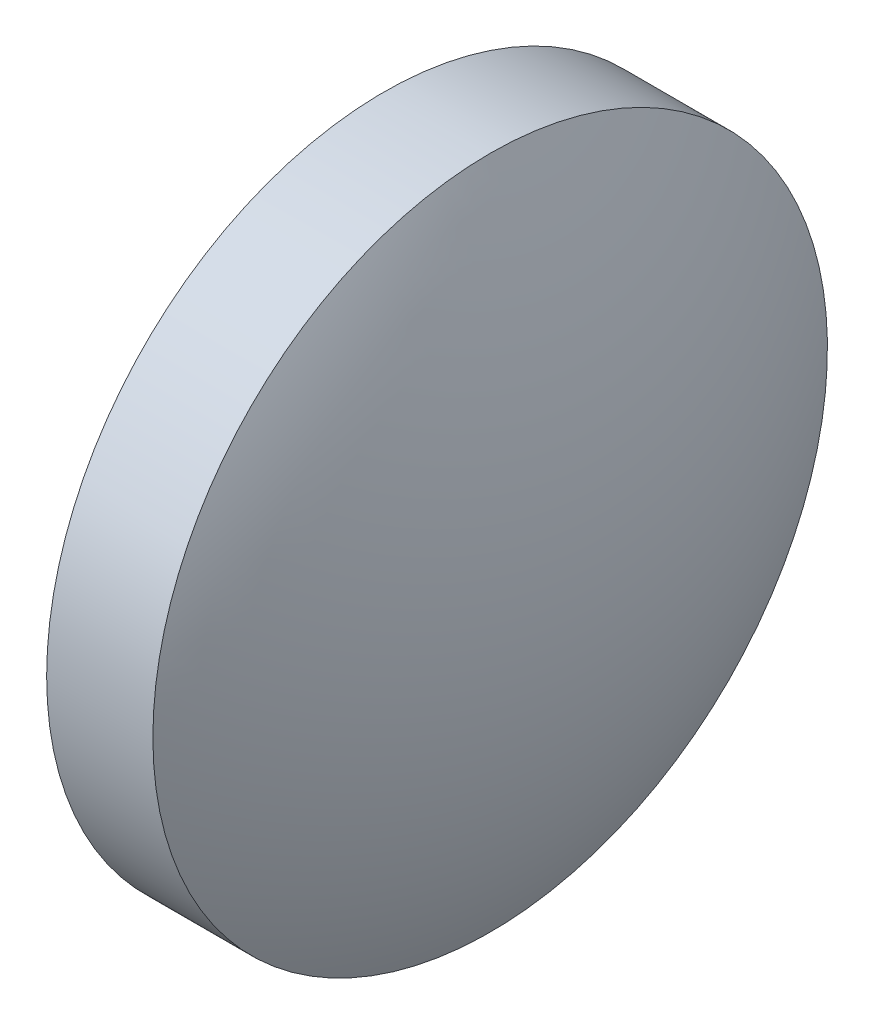
SolidWorks part; units mm, degrees
ref_plane "前视基准面" through (0, 0, 0) normal (0, 0, 1) x (1, 0, 0)
ref_plane "上视基准面" through (0, 0, 0) normal (0, 1, 0) x (1, 0, 0)
ref_plane "右视基准面" through (0, 0, 0) normal (1, 0, 0) x (0, 0, -1)
sketch "草图1" plane through (0, 0, 0) normal (0, 0, 1) x (1, 0, 0)
  line L0 (364.8813, 34.6953) -> (376.1845, 34.6953) construction
  line L1 (367.2093, 34.6953) -> (367.2093, 41.0453)
  line L2 (367.2093, 41.0453) -> (369.2093, 41.0453)
  line L3 (370.7693, 34.6953) -> (367.2093, 34.6953)
  arc A0 (370.7693, 34.6953) -> (369.2093, 41.0453) centre (357.0654, 34.6953) ccw
revolve "旋转1" add sketch "草图1" angle 360 about L0
